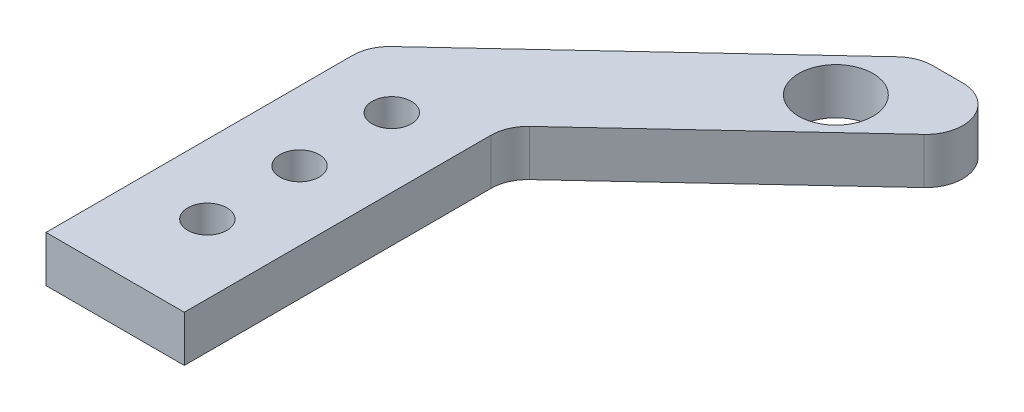
SolidWorks part; units mm, degrees
ref_plane "Front Plane" through (0, 0, 0) normal (0, 0, 1) x (1, 0, 0)
ref_plane "Top Plane" through (0, 0, 0) normal (0, 1, 0) x (1, 0, 0)
ref_plane "Right Plane" through (0, 0, 0) normal (1, 0, 0) x (0, 0, -1)
sketch "Sketch1" plane through (0, 0, 0) normal (0, 1, 0) x (1, 0, 0)
  line L0 (0, 0) -> (-65, 0) construction
  line L1 (-65, 0) -> (-65, 25) construction
  line L2 (0, 0) -> (-42.5847, 50.7504) construction
  line L3 (-72.5, 30) -> (-57.5, 30) construction
  line L4 (-57.5, 30) -> (-72.5, 30) construction
  line L5 (-57.5, 30) -> (-57.5, -5)
  line L6 (-57.5, -5) -> (-72.5, -5)
  line L7 (-72.5, 30) -> (-72.5, -5)
  line L8 (-65, -5) -> (-65, 30) construction
  line L9 (-57.5, 12.5) -> (-72.5, 12.5) construction
  line L10 (-72.5, 30) -> (-41.6608, 58.7504)
  line L11 (-57.5, 30) -> (-26.6608, 58.7504)
  line L12 (-41.6608, 58.7504) -> (-26.6608, 58.7504)
  circle A0 centre (0, 0) radius 55 construction
  circle A1 centre (0, 0) radius 62.5 construction
  circle A2 centre (-42.5847, 50.7504) radius 3.75 construction
  circle A3 centre (-65, 25) radius 2.125
  circle A4 centre (-65, 15) radius 2.125
  circle A5 centre (-42.5847, 50.7504) radius 4.025
  circle A6 centre (-65, 5) radius 2.125
  point P7 (-65, 0)
  point P9 (-65, 12.5)
  point P21 (-44.1647, 59.1161)
  point P22 (-41.6608, 58.7504)
  dimension "D1" = 110
  dimension "D4" = 125
  dimension "D5" = 7.5
  dimension "D11" = 4.25
  dimension "D12" = 10
  dimension "D13" = 8.05
  dimension "D15" = 10
  dimension "D2" = 25
  dimension "D3" = 65
  dimension "D6" = 66.25
  dimension "D7" = 50
  dimension "D8" = 15
  dimension "D9" = 5
  dimension "D10" = 35
  dimension "D14" = 8
extrude "Boss-Extrude1" add sketch "Sketch1" along normal mid plane 5
fillet "Fillet1" radius 4 4 edges at (-72.5, 0, -30) (-41.6608, 0, -58.7504) (-57.5, 0, -30) (-26.6608, 0, -58.7504)
